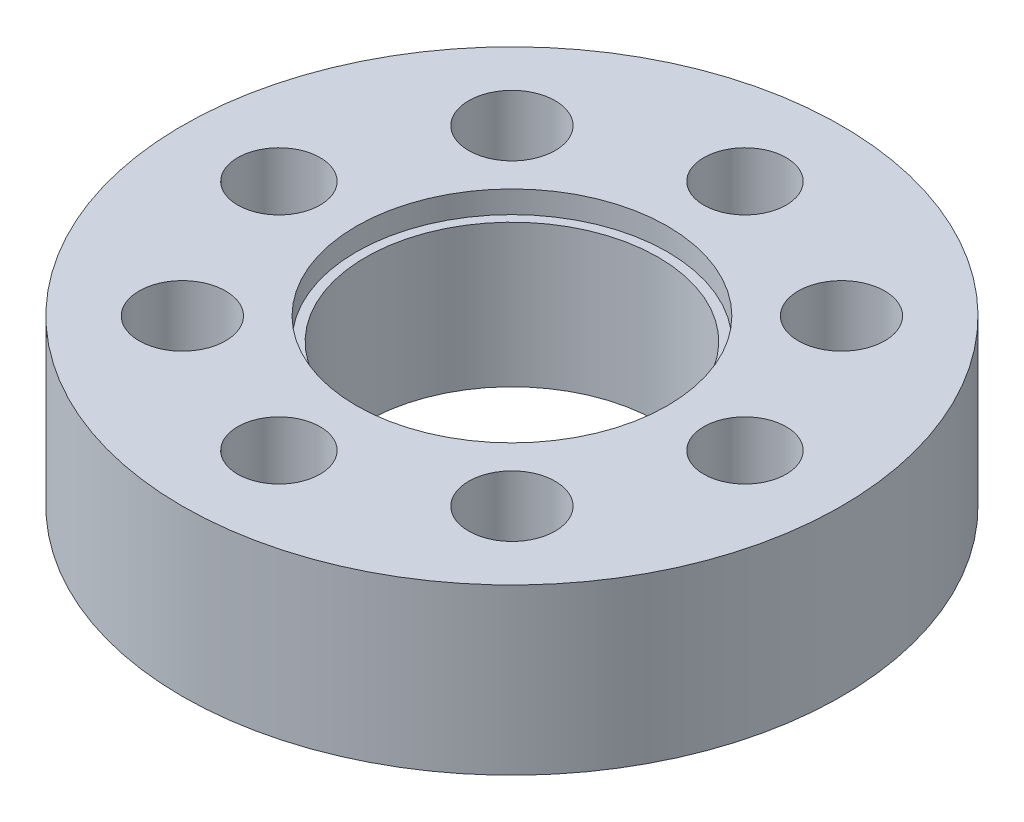
SolidWorks part; units mm, degrees
ref_plane "Front Plane" through (0, 0, 0) normal (0, 0, 1) x (1, 0, 0)
ref_plane "Top Plane" through (0, 0, 0) normal (0, 1, 0) x (1, 0, 0)
ref_plane "Right Plane" through (0, 0, 0) normal (1, 0, 0) x (0, 0, -1)
sketch "Sketch1" plane through (0, 0, 0) normal (0, 1, 0) x (1, 0, 0)
  line L1 (-8, 8) -> (8, 8) construction
  line L2 (-8, 8) -> (-8, -8) construction
  line L3 (-8, -8) -> (8, -8) construction
  line L4 (8, 8) -> (8, -8) construction
  line L5 (-8, 8) -> (8, -8) construction
  line L6 (-8, -8) -> (8, 8) construction
  circle A0 centre (0, 0) radius 16
  circle A1 centre (-8, 8) radius 2.1
  circle A2 centre (8, 8) radius 2.1
  circle A3 centre (8, -8) radius 2.1
  circle A4 centre (-8, -8) radius 2.1
  circle A5 centre (11.3137, 0) radius 2
  circle A6 centre (8, -8) radius 2.1
  circle A7 centre (0, -11.3137) radius 2
  circle A8 centre (-8, -8) radius 2.1
  circle A9 centre (-11.3137, 0) radius 2
  circle A10 centre (-8, 8) radius 2.1
  circle A11 centre (0, 11.3137) radius 2
  circle A12 centre (0, 0) radius 7.1
  point P27 (0, 0)
  dimension "D1" = 32
  dimension "D4" = 4.2
  dimension "D6" = 14.2
  dimension "D5" = 4
  dimension "D2" = 16
  dimension "D3" = 16
extrude "Boss-Extrude1" add sketch "Sketch1" along normal blind 8 contours A0 A12 A11 A9 A7 A5 A4 A3 A2 A1
sketch "Sketch2" plane through (0, 8, 0) normal (0, 1, 0) x (1, 0, 0)
  circle A0 centre (0, 0) radius 7.55
  dimension "D1" = 15.1
extrude "Cut-Extrude1" cut sketch "Sketch2" against normal blind 1.08
